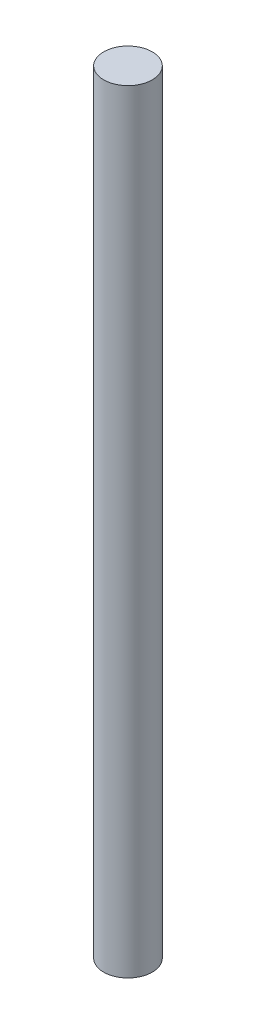
SolidWorks part; units mm, degrees
ref_plane "Front Plane" through (0, 0, 0) normal (0, 0, 1) x (1, 0, 0)
ref_plane "Top Plane" through (0, 0, 0) normal (0, 1, 0) x (1, 0, 0)
ref_plane "Right Plane" through (0, 0, 0) normal (1, 0, 0) x (0, 0, -1)
sketch "Sketch1" plane through (0, 0, 0) normal (0, 1, 0) x (1, 0, 0)
  circle A0 centre (0, 0) radius 27.5
  dimension "D1" = 55
extrude "Boss-Extrude1" add sketch "Sketch1" along normal blind 875
